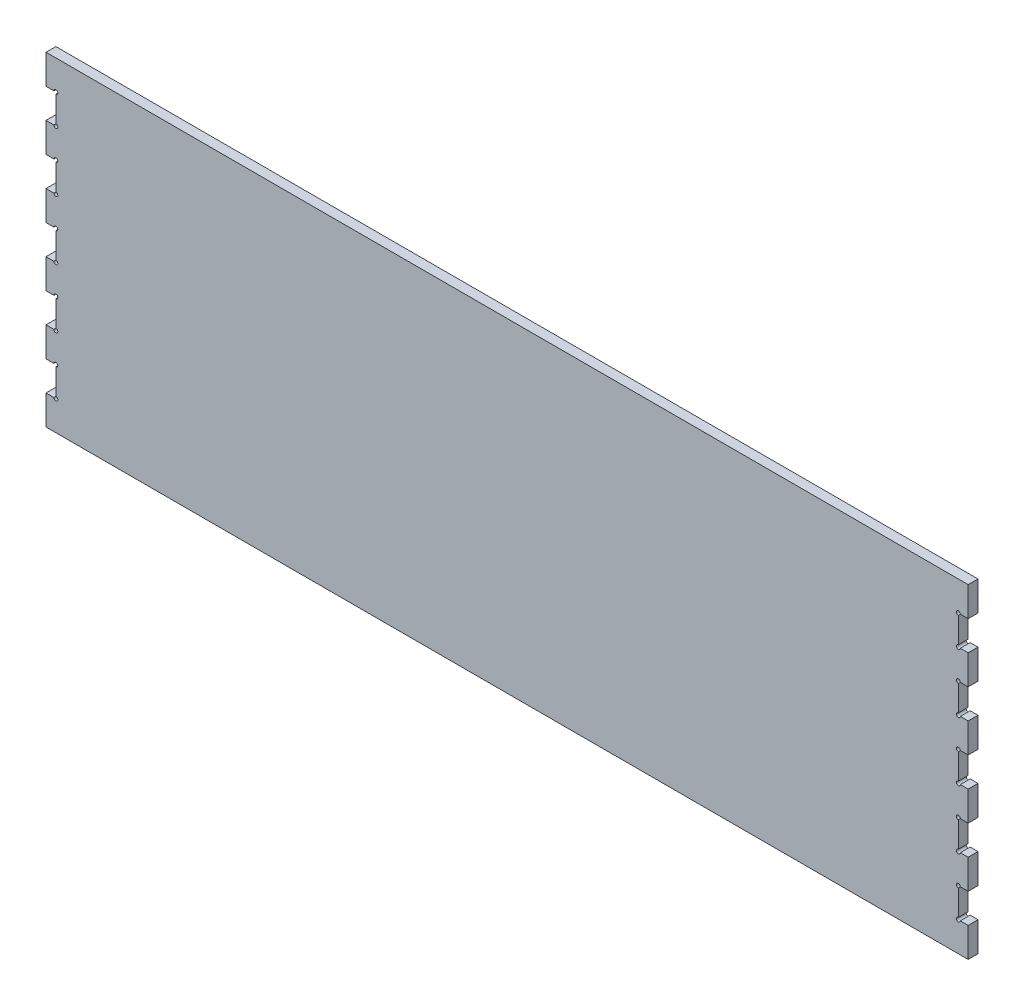
SolidWorks part; units mm, degrees
ref_plane "Front Plane" through (0, 0, 0) normal (0, 0, 1) x (1, 0, 0)
ref_plane "Top Plane" through (0, 0, 0) normal (0, 1, 0) x (1, 0, 0)
ref_plane "Right Plane" through (0, 0, 0) normal (1, 0, 0) x (0, 0, -1)
sketch "Sketch1" plane through (0, 0, 0) normal (0, 0, 1) x (1, 0, 0)
  line L0 (562.6644, 109.8333) -> (553.0644, 109.8333)
  line L1 (-562.3356, 145.8333) -> (562.6644, 145.8333)
  line L2 (-562.3356, 145.8333) -> (-562.3356, 109.8333)
  line L3 (562.6644, -70.1667) -> (562.6644, -106.1667)
  line L4 (562.6644, 145.8333) -> (562.6644, 109.8333)
  line L5 (562.6644, 109.8333) -> (562.6644, 73.8333) construction
  line L6 (553.0644, 73.8333) -> (562.6644, 73.8333)
  line L7 (562.6644, 73.8333) -> (562.6644, 37.8333)
  line L8 (562.6644, 37.8333) -> (553.0644, 37.8333)
  line L9 (550.6644, 35.4333) -> (550.6644, 4.2333)
  line L10 (553.0644, 1.8333) -> (562.6644, 1.8333)
  line L11 (562.6644, 1.8333) -> (562.6644, -34.1667)
  line L12 (0.1644, 145.8333) -> (0.1644, -34.1667) construction
  line L13 (550.6644, 109.8333) -> (553.0644, 109.8333) construction
  line L14 (553.0644, 109.8333) -> (551.8644, 109.8333) construction
  line L15 (551.8644, 109.8333) -> (551.8644, 108.3121) construction
  line L16 (550.6644, 109.8333) -> (550.6644, 107.4654) construction
  line L17 (550.6644, 107.4654) -> (550.6644, 108.6494) construction
  line L18 (550.6644, 108.6494) -> (552.3781, 108.6494) construction
  line L19 (550.6644, 107.4333) -> (550.6644, 76.2333)
  line L20 (562.6644, 91.8333) -> (477.4786, 91.8333) construction
  line L21 (562.6644, 73.8333) -> (562.6644, 37.8333) construction
  line L22 (562.6644, 55.8333) -> (455.7888, 55.8333) construction
  line L23 (562.6644, 1.8333) -> (562.6644, 37.8333) construction
  line L24 (562.6644, 19.8333) -> (434.4777, 19.8333) construction
  line L25 (-562.3356, -214.1667) -> (-552.7356, -214.1667)
  line L26 (-550.3356, -211.7667) -> (-550.3356, -180.5667)
  line L27 (-552.7356, -178.1667) -> (-562.3356, -178.1667)
  line L28 (-562.3356, -142.1667) -> (-552.7356, -142.1667)
  line L29 (-550.3356, -139.7667) -> (-550.3356, -108.5667)
  line L30 (-552.7356, -106.1667) -> (-562.3356, -106.1667)
  line L31 (-562.3356, -70.1667) -> (-552.7356, -70.1667)
  line L32 (-550.3356, -36.5667) -> (-550.3356, -67.7667)
  line L33 (562.6644, -250.1667) -> (-562.3356, -250.1667)
  line L34 (-562.3356, -34.1667) -> (-552.7356, -34.1667)
  line L35 (562.6644, -34.1667) -> (553.0644, -34.1667)
  line L36 (550.6644, -36.5667) -> (550.6644, -67.7667)
  line L37 (-552.7356, 1.8333) -> (-562.3356, 1.8333)
  line L38 (491.1756, 1.8333) -> (491.0394, -34.1667) construction
  line L39 (491.0394, -34.1667) -> (491.1075, -16.1667) construction
  line L40 (491.1075, -16.1667) -> (467.63, -16.1667) construction
  line L41 (379.2279, 145.8333) -> (379.2279, -250.1667) construction
  line L42 (379.2279, -250.1667) -> (379.2279, -52.1667) construction
  line L43 (379.2279, -52.1667) -> (612.9887, -52.1667) construction
  line L44 (562.6644, -214.1667) -> (553.0644, -214.1667)
  line L45 (550.6644, -211.7667) -> (550.6644, -180.5667)
  line L46 (553.0644, -178.1667) -> (562.6644, -178.1667)
  line L47 (562.6644, -142.1667) -> (553.0644, -142.1667)
  line L48 (550.6644, -139.7667) -> (550.6644, -108.5667)
  line L49 (553.0644, -106.1667) -> (562.6644, -106.1667)
  line L50 (562.6644, -70.1667) -> (553.0644, -70.1667)
  line L51 (562.6644, -142.1667) -> (562.6644, -178.1667)
  line L52 (562.6644, -214.1667) -> (562.6644, -250.1667)
  line L53 (-550.3356, 35.4333) -> (-550.3356, 4.2333)
  line L54 (-562.3356, 37.8333) -> (-552.7356, 37.8333)
  line L55 (-552.7356, 73.8333) -> (-562.3356, 73.8333)
  line L56 (-550.3356, 107.4333) -> (-550.3356, 76.2333)
  line L57 (-562.3356, 109.8333) -> (-552.7356, 109.8333)
  line L58 (-562.3356, 73.8333) -> (-562.3356, 37.8333)
  line L59 (-562.3356, 1.8333) -> (-562.3356, -34.1667)
  line L60 (-562.3356, -70.1667) -> (-562.3356, -106.1667)
  line L61 (-562.3356, -142.1667) -> (-562.3356, -178.1667)
  line L62 (-562.3356, -214.1667) -> (-562.3356, -250.1667)
  arc A0 (553.0644, 109.8333) -> (550.6644, 107.4333) centre (550.6644, 109.8333) ccw
  arc A1 (553.0644, 73.8333) -> (550.6644, 76.2333) centre (550.6644, 73.8333) cw
  arc A2 (553.0644, 37.8333) -> (550.6644, 35.4333) centre (550.6644, 37.8333) ccw
  arc A3 (553.0644, 1.8333) -> (550.6644, 4.2333) centre (550.6644, 1.8333) cw
  arc A4 (-552.7356, -214.1667) -> (-550.3356, -211.7667) centre (-550.3356, -214.1667) ccw
  arc A5 (-552.7356, -178.1667) -> (-550.3356, -180.5667) centre (-550.3356, -178.1667) cw
  arc A6 (-552.7356, -142.1667) -> (-550.3356, -139.7667) centre (-550.3356, -142.1667) ccw
  arc A7 (-552.7356, -106.1667) -> (-550.3356, -108.5667) centre (-550.3356, -106.1667) cw
  arc A8 (553.0644, -34.1667) -> (550.6644, -36.5667) centre (550.6644, -34.1667) ccw
  arc A9 (553.0644, -214.1667) -> (550.6644, -211.7667) centre (550.6644, -214.1667) cw
  arc A10 (553.0644, -178.1667) -> (550.6644, -180.5667) centre (550.6644, -178.1667) ccw
  arc A11 (553.0644, -142.1667) -> (550.6644, -139.7667) centre (550.6644, -142.1667) cw
  arc A12 (553.0644, -106.1667) -> (550.6644, -108.5667) centre (550.6644, -106.1667) ccw
  arc A13 (553.0644, -70.1667) -> (550.6644, -67.7667) centre (550.6644, -70.1667) cw
  arc A14 (-552.7356, -70.1667) -> (-550.3356, -67.7667) centre (-550.3356, -70.1667) ccw
  arc A15 (-552.7356, -34.1667) -> (-550.3356, -36.5667) centre (-550.3356, -34.1667) cw
  arc A16 (-552.7356, 1.8333) -> (-550.3356, 4.2333) centre (-550.3356, 1.8333) ccw
  arc A17 (-552.7356, 37.8333) -> (-550.3356, 35.4333) centre (-550.3356, 37.8333) cw
  arc A18 (-552.7356, 73.8333) -> (-550.3356, 76.2333) centre (-550.3356, 73.8333) ccw
  arc A19 (-552.7356, 109.8333) -> (-550.3356, 107.4333) centre (-550.3356, 109.8333) cw
  dimension "D10" = 4.8
  dimension "D1" = 1125
  dimension "D2" = 36
  dimension "D3" = 36
  dimension "D4" = 36
  dimension "D5" = 12
  dimension "D6" = 36
  dimension "D9" = 36
  dimension "D11" = 36
extrude "Boss-Extrude1" add sketch "Sketch1" along normal blind 12
sketch "Sketch4" plane through (0, 0, 12) normal (0, 0, 1) x (1, 0, 0)
  line L44 (-562.3356, 145.8333) -> (-562.3356, 109.8333)
  line L45 (-562.3356, 109.8333) -> (-552.7356, 109.8333)
  line L46 (-550.3356, 107.4333) -> (-550.3356, 76.2333)
  line L47 (-552.7356, 73.8333) -> (-562.3356, 73.8333)
  line L48 (-562.3356, 73.8333) -> (-562.3356, 37.8333)
  line L49 (-562.3356, 37.8333) -> (-552.7356, 37.8333)
  line L50 (-550.3356, 35.4333) -> (-550.3356, 4.2333)
  line L51 (-552.7356, 1.8333) -> (-562.3356, 1.8333)
  line L52 (-562.3356, 1.8333) -> (-562.3356, -34.1667)
  line L53 (-562.3356, -34.1667) -> (-552.7356, -34.1667)
  line L54 (-550.3356, -36.5667) -> (-550.3356, -67.7667)
  line L55 (-552.7356, -70.1667) -> (-562.3356, -70.1667)
  line L56 (-562.3356, -70.1667) -> (-562.3356, -106.1667)
  line L57 (-562.3356, -106.1667) -> (-552.7356, -106.1667)
  line L58 (-550.3356, -108.5667) -> (-550.3356, -139.7667)
  line L59 (-552.7356, -142.1667) -> (-562.3356, -142.1667)
  line L60 (-562.3356, -142.1667) -> (-562.3356, -178.1667)
  line L61 (-562.3356, -178.1667) -> (-552.7356, -178.1667)
  line L62 (-550.3356, -180.5667) -> (-550.3356, -211.7667)
  line L63 (-552.7356, -214.1667) -> (-562.3356, -214.1667)
  line L64 (-562.3356, -214.1667) -> (-562.3356, -250.1667)
  line L65 (-562.3356, -250.1667) -> (562.6644, -250.1667)
  line L66 (562.6644, -250.1667) -> (562.6644, -214.1667)
  line L67 (562.6644, -214.1667) -> (553.0644, -214.1667)
  line L68 (550.6644, -211.7667) -> (550.6644, -180.5667)
  line L69 (553.0644, -178.1667) -> (562.6644, -178.1667)
  line L70 (562.6644, -178.1667) -> (562.6644, -142.1667)
  line L71 (562.6644, -142.1667) -> (553.0644, -142.1667)
  line L72 (550.6644, -139.7667) -> (550.6644, -108.5667)
  line L73 (553.0644, -106.1667) -> (562.6644, -106.1667)
  line L74 (562.6644, -106.1667) -> (562.6644, -70.1667)
  line L75 (562.6644, -70.1667) -> (553.0644, -70.1667)
  line L76 (550.6644, -67.7667) -> (550.6644, -36.5667)
  line L77 (553.0644, -34.1667) -> (562.6644, -34.1667)
  line L78 (562.6644, -34.1667) -> (562.6644, 1.8333)
  line L79 (562.6644, 1.8333) -> (553.0644, 1.8333)
  line L80 (550.6644, 4.2333) -> (550.6644, 35.4333)
  line L81 (553.0644, 37.8333) -> (562.6644, 37.8333)
  line L82 (562.6644, 37.8333) -> (562.6644, 73.8333)
  line L83 (562.6644, 73.8333) -> (553.0644, 73.8333)
  line L84 (550.6644, 76.2333) -> (550.6644, 107.4333)
  line L85 (553.0644, 109.8333) -> (562.6644, 109.8333)
  line L86 (562.6644, 109.8333) -> (562.6644, 145.8333)
  line L87 (562.6644, 145.8333) -> (-562.3356, 145.8333)
  line L88 (-562.3356, 145.8333) -> (-562.3356, 109.8333)
  line L89 (-562.3356, 109.8333) -> (-552.7356, 109.8333)
  line L90 (-550.3356, 107.4333) -> (-550.3356, 76.2333)
  line L91 (-552.7356, 73.8333) -> (-562.3356, 73.8333)
  line L92 (-562.3356, 73.8333) -> (-562.3356, 37.8333)
  line L93 (-562.3356, 37.8333) -> (-552.7356, 37.8333)
  line L94 (-550.3356, 35.4333) -> (-550.3356, 4.2333)
  line L95 (-552.7356, 1.8333) -> (-562.3356, 1.8333)
  line L96 (-562.3356, 1.8333) -> (-562.3356, -34.1667)
  line L97 (-562.3356, -34.1667) -> (-552.7356, -34.1667)
  line L98 (-550.3356, -36.5667) -> (-550.3356, -67.7667)
  line L99 (-552.7356, -70.1667) -> (-562.3356, -70.1667)
  line L100 (-562.3356, -70.1667) -> (-562.3356, -106.1667)
  line L101 (-562.3356, -106.1667) -> (-552.7356, -106.1667)
  line L102 (-550.3356, -108.5667) -> (-550.3356, -139.7667)
  line L103 (-552.7356, -142.1667) -> (-562.3356, -142.1667)
  line L104 (-562.3356, -142.1667) -> (-562.3356, -178.1667)
  line L105 (-562.3356, -178.1667) -> (-552.7356, -178.1667)
  line L106 (-550.3356, -180.5667) -> (-550.3356, -211.7667)
  line L107 (-552.7356, -214.1667) -> (-562.3356, -214.1667)
  line L108 (-562.3356, -214.1667) -> (-562.3356, -250.1667)
  line L109 (-562.3356, -250.1667) -> (562.6644, -250.1667)
  line L110 (562.6644, -250.1667) -> (562.6644, -214.1667)
  line L111 (562.6644, -214.1667) -> (553.0644, -214.1667)
  line L112 (550.6644, -211.7667) -> (550.6644, -180.5667)
  line L113 (553.0644, -178.1667) -> (562.6644, -178.1667)
  line L114 (562.6644, -178.1667) -> (562.6644, -142.1667)
  line L115 (562.6644, -142.1667) -> (553.0644, -142.1667)
  line L116 (550.6644, -139.7667) -> (550.6644, -108.5667)
  line L117 (553.0644, -106.1667) -> (562.6644, -106.1667)
  line L118 (562.6644, -106.1667) -> (562.6644, -70.1667)
  line L119 (562.6644, -70.1667) -> (553.0644, -70.1667)
  line L120 (550.6644, -67.7667) -> (550.6644, -36.5667)
  line L121 (553.0644, -34.1667) -> (562.6644, -34.1667)
  line L122 (562.6644, -34.1667) -> (562.6644, 1.8333)
  line L123 (562.6644, 1.8333) -> (553.0644, 1.8333)
  line L124 (550.6644, 4.2333) -> (550.6644, 35.4333)
  line L125 (553.0644, 37.8333) -> (562.6644, 37.8333)
  line L126 (562.6644, 37.8333) -> (562.6644, 73.8333)
  line L127 (562.6644, 73.8333) -> (553.0644, 73.8333)
  line L128 (550.6644, 76.2333) -> (550.6644, 107.4333)
  line L129 (553.0644, 109.8333) -> (562.6644, 109.8333)
  line L130 (562.6644, 109.8333) -> (562.6644, 145.8333)
  line L131 (562.6644, 145.8333) -> (-562.3356, 145.8333)
  arc A20 (-550.3356, 107.4333) -> (-552.7356, 109.8333) centre (-550.3356, 109.8333) ccw
  arc A21 (-552.7356, 73.8333) -> (-550.3356, 76.2333) centre (-550.3356, 73.8333) ccw
  arc A22 (-550.3356, 35.4333) -> (-552.7356, 37.8333) centre (-550.3356, 37.8333) ccw
  arc A23 (-552.7356, 1.8333) -> (-550.3356, 4.2333) centre (-550.3356, 1.8333) ccw
  arc A24 (-550.3356, -36.5667) -> (-552.7356, -34.1667) centre (-550.3356, -34.1667) ccw
  arc A25 (-552.7356, -70.1667) -> (-550.3356, -67.7667) centre (-550.3356, -70.1667) ccw
  arc A26 (-550.3356, -108.5667) -> (-552.7356, -106.1667) centre (-550.3356, -106.1667) ccw
  arc A27 (-552.7356, -142.1667) -> (-550.3356, -139.7667) centre (-550.3356, -142.1667) ccw
  arc A28 (-550.3356, -180.5667) -> (-552.7356, -178.1667) centre (-550.3356, -178.1667) ccw
  arc A29 (-552.7356, -214.1667) -> (-550.3356, -211.7667) centre (-550.3356, -214.1667) ccw
  arc A30 (550.6644, -211.7667) -> (553.0644, -214.1667) centre (550.6644, -214.1667) ccw
  arc A31 (553.0644, -178.1667) -> (550.6644, -180.5667) centre (550.6644, -178.1667) ccw
  arc A32 (550.6644, -139.7667) -> (553.0644, -142.1667) centre (550.6644, -142.1667) ccw
  arc A33 (553.0644, -106.1667) -> (550.6644, -108.5667) centre (550.6644, -106.1667) ccw
  arc A34 (550.6644, -67.7667) -> (553.0644, -70.1667) centre (550.6644, -70.1667) ccw
  arc A35 (553.0644, -34.1667) -> (550.6644, -36.5667) centre (550.6644, -34.1667) ccw
  arc A36 (550.6644, 4.2333) -> (553.0644, 1.8333) centre (550.6644, 1.8333) ccw
  arc A37 (553.0644, 37.8333) -> (550.6644, 35.4333) centre (550.6644, 37.8333) ccw
  arc A38 (550.6644, 76.2333) -> (553.0644, 73.8333) centre (550.6644, 73.8333) ccw
  arc A39 (553.0644, 109.8333) -> (550.6644, 107.4333) centre (550.6644, 109.8333) ccw
  arc A40 (-550.3356, 107.4333) -> (-552.7356, 109.8333) centre (-550.3356, 109.8333) ccw
  arc A41 (-552.7356, 73.8333) -> (-550.3356, 76.2333) centre (-550.3356, 73.8333) ccw
  arc A42 (-550.3356, 35.4333) -> (-552.7356, 37.8333) centre (-550.3356, 37.8333) ccw
  arc A43 (-552.7356, 1.8333) -> (-550.3356, 4.2333) centre (-550.3356, 1.8333) ccw
  arc A44 (-550.3356, -36.5667) -> (-552.7356, -34.1667) centre (-550.3356, -34.1667) ccw
  arc A45 (-552.7356, -70.1667) -> (-550.3356, -67.7667) centre (-550.3356, -70.1667) ccw
  arc A46 (-550.3356, -108.5667) -> (-552.7356, -106.1667) centre (-550.3356, -106.1667) ccw
  arc A47 (-552.7356, -142.1667) -> (-550.3356, -139.7667) centre (-550.3356, -142.1667) ccw
  arc A48 (-550.3356, -180.5667) -> (-552.7356, -178.1667) centre (-550.3356, -178.1667) ccw
  arc A49 (-552.7356, -214.1667) -> (-550.3356, -211.7667) centre (-550.3356, -214.1667) ccw
  arc A50 (550.6644, -211.7667) -> (553.0644, -214.1667) centre (550.6644, -214.1667) ccw
  arc A51 (553.0644, -178.1667) -> (550.6644, -180.5667) centre (550.6644, -178.1667) ccw
  arc A52 (550.6644, -139.7667) -> (553.0644, -142.1667) centre (550.6644, -142.1667) ccw
  arc A53 (553.0644, -106.1667) -> (550.6644, -108.5667) centre (550.6644, -106.1667) ccw
  arc A54 (550.6644, -67.7667) -> (553.0644, -70.1667) centre (550.6644, -70.1667) ccw
  arc A55 (553.0644, -34.1667) -> (550.6644, -36.5667) centre (550.6644, -34.1667) ccw
  arc A56 (550.6644, 4.2333) -> (553.0644, 1.8333) centre (550.6644, 1.8333) ccw
  arc A57 (553.0644, 37.8333) -> (550.6644, 35.4333) centre (550.6644, 37.8333) ccw
  arc A58 (550.6644, 76.2333) -> (553.0644, 73.8333) centre (550.6644, 73.8333) ccw
  arc A59 (553.0644, 109.8333) -> (550.6644, 107.4333) centre (550.6644, 109.8333) ccw
  dimension "D1" = 0
